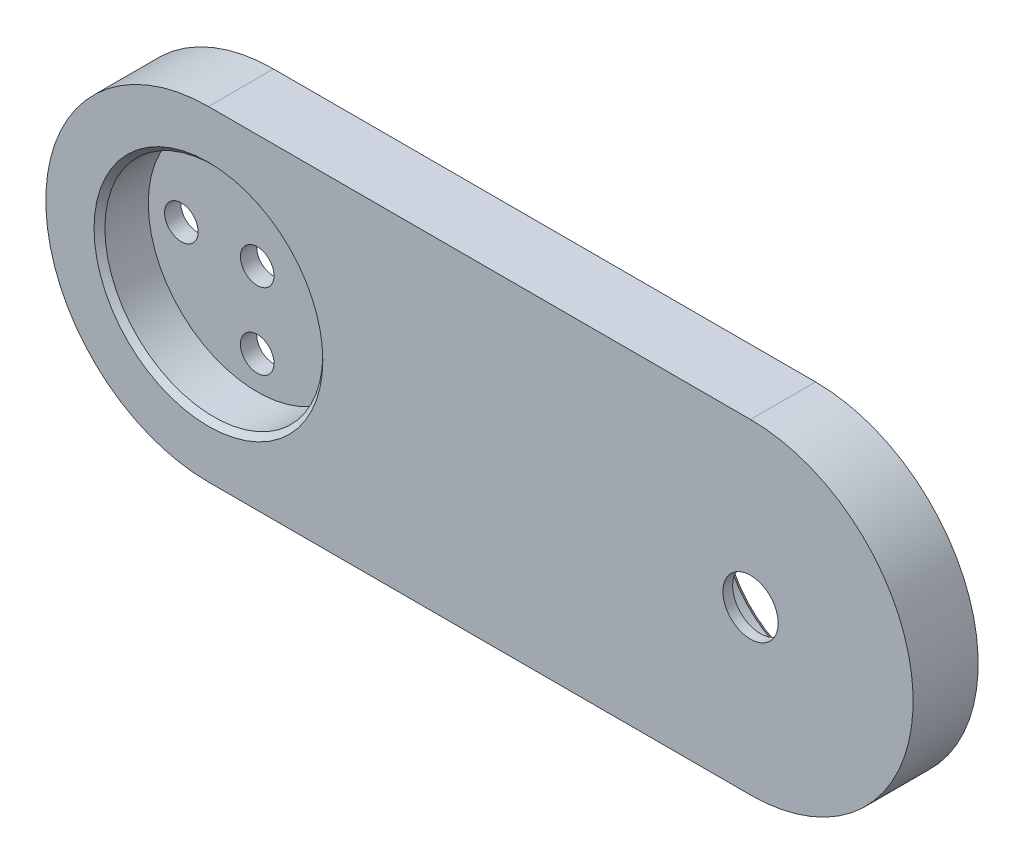
SolidWorks part; units mm, degrees
ref_plane "Front Plane" through (0, 0, 0) normal (0, 0, 1) x (1, 0, 0)
ref_plane "Top Plane" through (0, 0, 0) normal (0, 1, 0) x (1, 0, 0)
ref_plane "Right Plane" through (0, 0, 0) normal (1, 0, 0) x (0, 0, -1)
sketch "Sketch4" plane through (0, 0, 0) normal (0, 0, 1) x (1, 0, 0)
  line L0 (-25, 15) -> (25, 15)
  line L1 (25, -15) -> (-25, -15)
  line L2 (-25, 0) -> (25, 0) construction
  arc A0 (25, 15) -> (25, -15) centre (25, 0) cw
  arc A1 (-25, -15) -> (-25, 15) centre (-25, 0) cw
  dimension "D2" = 15
  dimension "D1" = 50
extrude "Boss-Extrude1" add sketch "Sketch4" along normal blind 6
sketch "Sketch8" plane through (0, 0, 6) normal (0, 0, 1) x (1, 0, 0)
  circle A0 centre (-25, 0) radius 10.05
  dimension "D1" = 20.1
extrude "Cut-Extrude4" cut sketch "Sketch8" against normal blind 4.5
sketch "Sketch9" plane through (0, 0, 0) normal (0, 0, -1) x (-1, 0, 0)
  circle A0 centre (-25, 0) radius 7.975
  dimension "D1" = 15.95
extrude "Cut-Extrude5" cut sketch "Sketch9" against normal blind 5.1
sketch "Sketch10" plane through (0, 0, 5.1) normal (0, 0, -1) x (-1, 0, 0)
  circle A0 centre (-25, 0) radius 2.55
  dimension "D1" = 5.1
extrude "Cut-Extrude6" cut sketch "Sketch10" against normal through all
sketch "Sketch11" plane through (0, 0, 1.5) normal (0, 0, 1) x (1, 0, 0)
  line L0 (-32, 0) -> (-18, 0) construction
  line L1 (-25, -7) -> (-25, 7) construction
  circle A0 centre (-25, 0) radius 1.55
  circle A1 centre (-18, 0) radius 1.55
  circle A2 centre (-32, 0) radius 1.55
  circle A3 centre (-25, 7) radius 1.55
  circle A4 centre (-25, -7) radius 1.55
  dimension "D1" = 3.1
  dimension "D2" = 14
extrude "Cut-Extrude7" cut sketch "Sketch11" against normal through all
chamfer "Chamfer1" distance 0.5 angle 45 2 edges at (17.025, 0, 0) (-14.95, 0, 6)
